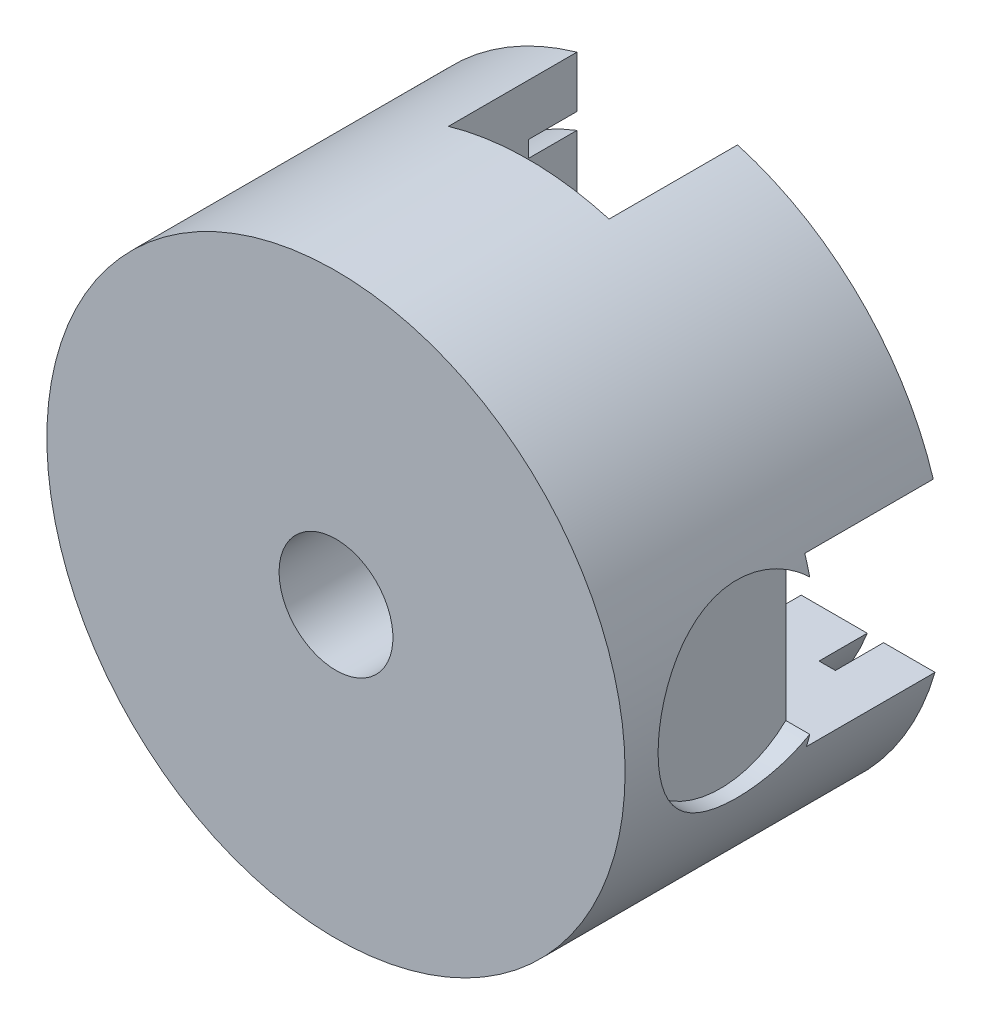
SolidWorks part; units mm, degrees
ref_plane "Front Plane" through (0, 0, 0) normal (0, 0, 1) x (1, 0, 0)
ref_plane "Top Plane" through (0, 0, 0) normal (0, 1, 0) x (1, 0, 0)
ref_plane "Right Plane" through (0, 0, 0) normal (1, 0, 0) x (0, 0, -1)
sketch "Sketch1" plane through (0, 0, 0) normal (0, 0, 1) x (1, 0, 0)
  circle A0 centre (0, 0) radius 180
  dimension "D1" = 360
extrude "Boss-Extrude1" add sketch "Sketch1" along normal blind 200
sketch "Sketch2" plane through (0, 0, 0) normal (0, 0, -1) x (-1, 0, 0)
  line L0 (50, -50) -> (50, -249.8325)
  line L1 (-50, 228.0356) -> (50, 228.0356)
  line L2 (-50, 228.0356) -> (-50, 53.6137)
  line L3 (-50, -249.8325) -> (50, -249.8325)
  line L4 (50, 228.0356) -> (50, 53.6137)
  line L5 (-236.1193, 53.6137) -> (-50, 53.6137)
  line L6 (-236.1193, 53.6137) -> (-236.1193, -50)
  line L7 (-236.1193, -50) -> (-50, -50)
  line L8 (294.3144, 53.6137) -> (294.3144, -50)
  line L9 (-50, -50) -> (-50, -249.8325)
  line L10 (50, 53.6137) -> (294.3144, 53.6137)
  line L11 (50, -50) -> (294.3144, -50)
  dimension "D1" = 50
  dimension "D2" = 50
  dimension "D3" = 53.6137
  dimension "D4" = 50
extrude "Cut-Extrude1" cut sketch "Sketch2" against normal blind 80
sketch "Sketch6" plane through (0, 0, 0) normal (0, 0, -1) x (-1, 0, 0)
  circle A0 centre (0, 0) radius 35.4321
extrude "Cut-Extrude4" cut sketch "Sketch6" against normal through all
sketch "Sketch7" plane through (0, 0, 0) normal (0, 0, -1) x (-1, 0, 0)
  circle A0 centre (0, 0) radius 149.5105
  circle A1 centre (0, 0) radius 139.9639
  circle A2 centre (0, 0) radius 102.6295
  circle A3 centre (0, 0) radius 93.7288
extrude "Cut-Extrude6" cut sketch "Sketch7" against normal blind 30
sketch "Sketch8" plane through (0, 0, 0) normal (1, 0, 0) x (0, 0, -1)
  circle A0 centre (-120.6946, 0) radius 58.7787
extrude "Cut-Extrude7" cut sketch "Sketch8" against normal blind 30 from offset 190
sketch "Sketch9" plane through (0, 0, 0) normal (1, 0, 0) x (0, 0, -1)
  circle A0 centre (-120.6946, 0) radius 58.7787
extrude "Cut-Extrude8" cut sketch "Sketch9" against normal blind 236 from offset 150 offset against normal yes
